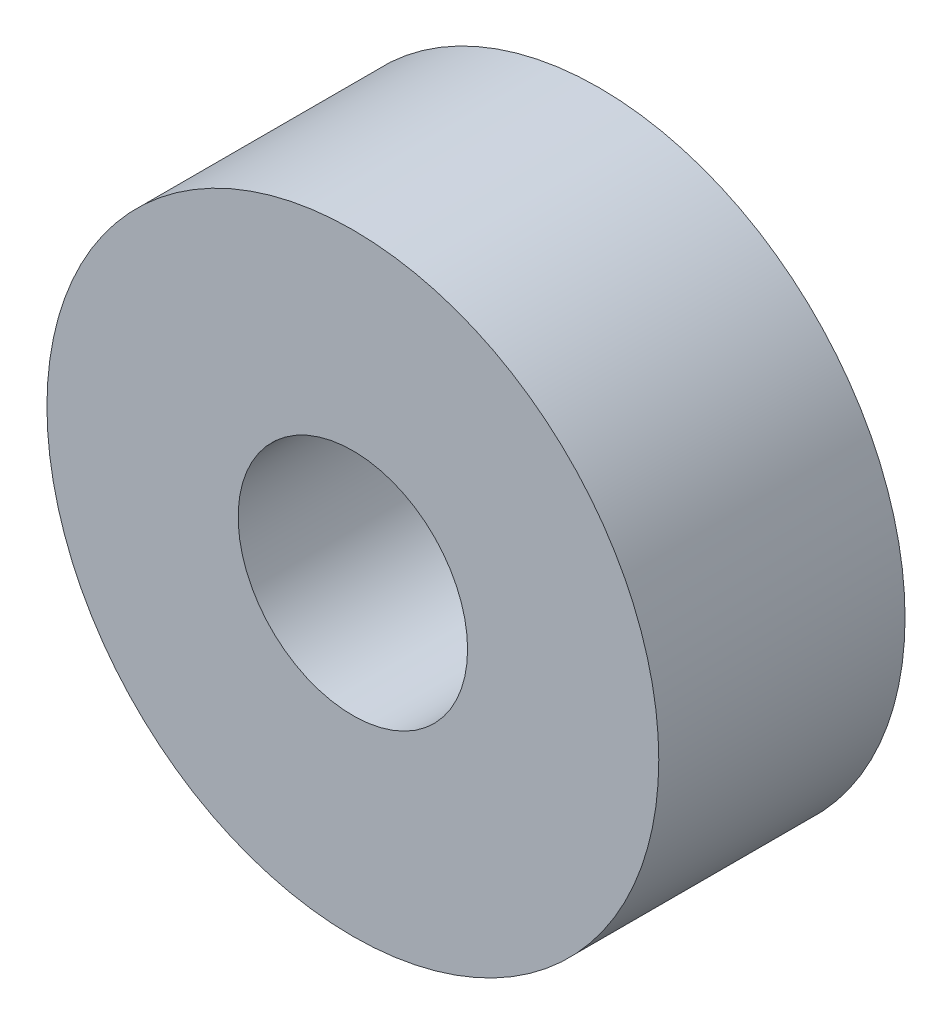
SolidWorks part; units mm, degrees
ref_plane "Front Plane" through (0, 0, 0) normal (0, 0, 1) x (1, 0, 0)
ref_plane "Top Plane" through (0, 0, 0) normal (0, 1, 0) x (1, 0, 0)
ref_plane "Right Plane" through (0, 0, 0) normal (1, 0, 0) x (0, 0, -1)
sketch "Sketch1" plane through (0, 0, 0) normal (0, 0, 1) x (1, 0, 0)
  circle A0 centre (0, 0) radius 1.5
  circle A1 centre (0, 0) radius 4
  dimension "D1" = 3
  dimension "D2" = 8
extrude "Boss-Extrude1" add sketch "Sketch1" along normal mid plane 3.22
